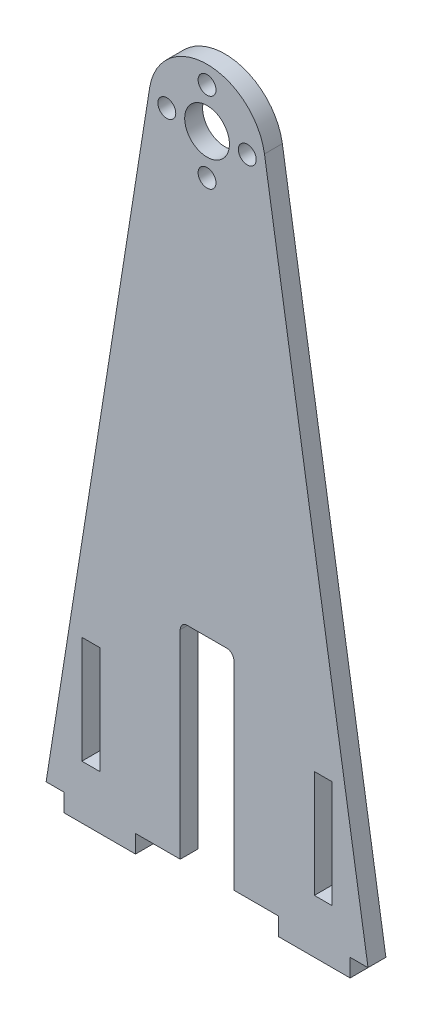
SolidWorks part; units mm, degrees
material "Pine"
ref_plane "Front Plane" through (0, 0, 0) normal (0, 0, 1) x (1, 0, 0)
ref_plane "Top Plane" through (0, 0, 0) normal (0, 1, 0) x (1, 0, 0)
ref_plane "Right Plane" through (0, 0, 0) normal (1, 0, 0) x (0, 0, -1)
sketch "Sketch1" plane through (0, 0, 0) normal (0, 0, 1) x (1, 0, 0)
  line L0 (0, 0) -> (0, 228.6) construction
  line L1 (25.4, 0) -> (9.525, 0)
  line L2 (-25.4, 0) -> (-25.4, -6.35)
  line L3 (-25.4, -6.35) -> (-50.8, -6.35)
  line L4 (-50.8, -6.35) -> (-50.8, 0)
  line L5 (-50.8, 0) -> (-57.15, 0)
  line L6 (-57.15, 0) -> (-20.3828, 231.8326)
  line L7 (0, 228.6) -> (0, 159.1888) construction
  line L8 (50.8, 0) -> (57.15, 0)
  line L9 (50.8, -6.35) -> (50.8, 0)
  line L10 (25.4, 0) -> (25.4, -6.35)
  line L11 (25.4, -6.35) -> (50.8, -6.35)
  line L12 (57.15, 0) -> (20.3828, 231.8326)
  line L13 (44.45, 12.7) -> (38.1, 12.7)
  line L14 (-44.45, 12.7) -> (-38.1, 12.7)
  line L15 (-44.45, 12.7) -> (-44.45, 50.8)
  line L16 (-44.45, 50.8) -> (-38.1, 50.8)
  line L17 (-38.1, 12.7) -> (-38.1, 50.8)
  line L22 (44.45, 12.7) -> (44.45, 50.8)
  line L23 (44.45, 50.8) -> (38.1, 50.8)
  line L24 (38.1, 12.7) -> (38.1, 50.8)
  line L25 (-9.525, 73.1663) -> (9.525, 73.1663)
  line L26 (9.525, 73.1663) -> (9.525, 0)
  line L27 (-38.1, 0) -> (-38.1, 12.7) construction
  line L28 (-44.45, 12.7) -> (-44.45, 0) construction
  line L30 (-9.525, 73.1663) -> (-9.525, 0)
  line L31 (-9.525, 0) -> (-25.4, 0)
  arc A0 (20.3828, 231.8326) -> (-20.3828, 231.8326) centre (0, 228.6) ccw
  circle A1 centre (0, 228.6) radius 7.9375
  circle A3 centre (0, 242.8875) radius 3.175
  circle A4 centre (14.2875, 228.6) radius 3.175
  circle A5 centre (0, 214.3125) radius 3.175
  circle A6 centre (-14.2875, 228.6) radius 3.175
  point P42 (0, 228.6)
  point P43 (0, 73.1663)
  dimension "D5" = 12.7
  dimension "D7" = 15.875
  dimension "D8" = 19.05
  dimension "D13" = 6.35
  dimension "D1" = 57.15
  dimension "D2" = 6.35
  dimension "D3" = 25.4
  dimension "D4" = 25.4
  dimension "D6" = 228.6
  dimension "D10" = 38.1
  dimension "D11" = 12.7
  dimension "D12" = 14.2875
  dimension "D14" = 4
extrude "Boss-Extrude1" add sketch "Sketch1" along normal blind 6.35
fillet "Fillet1" radius 2.54 1 edges at (-9.525, 73.1663, 3.175)
fillet "Fillet2" radius 2.54 1 edges at (9.525, 73.1663, 3.175)
